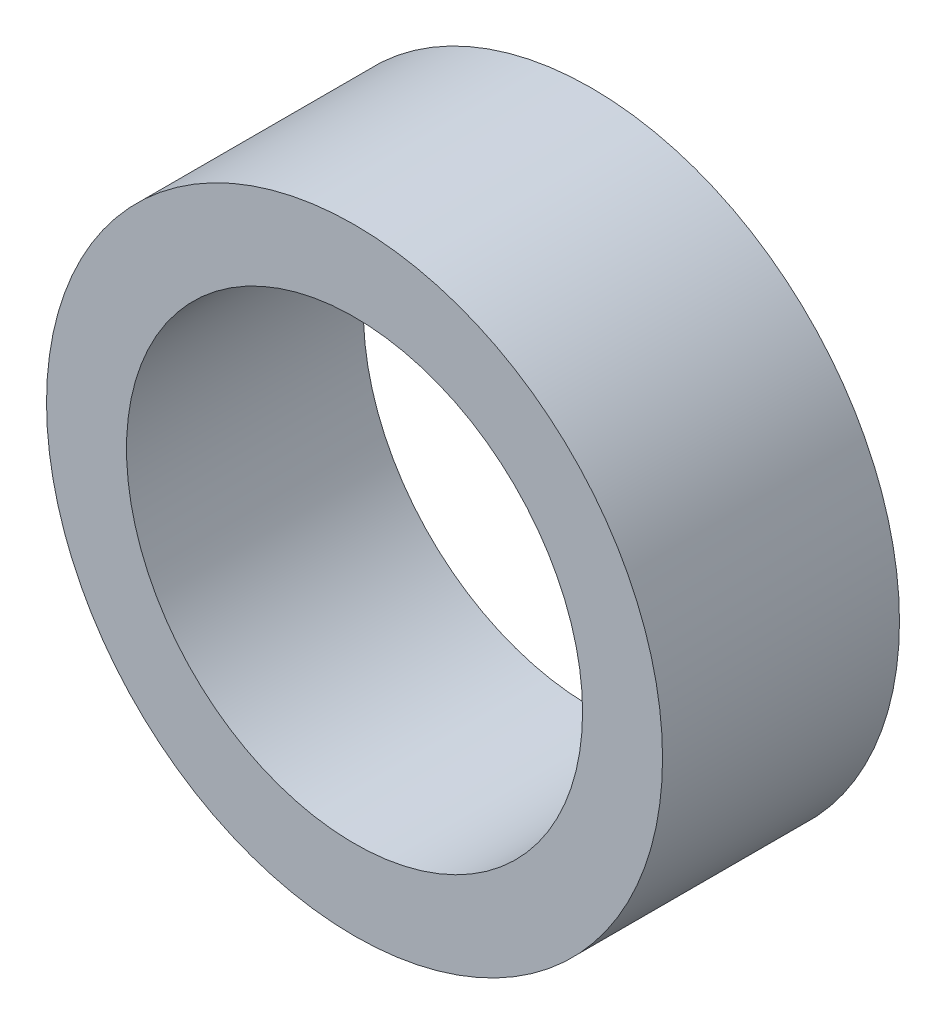
SolidWorks part; units mm, degrees
ref_plane "Piano frontale" through (0, 0, 0) normal (0, 0, 1) x (1, 0, 0)
ref_plane "Piano superiore" through (0, 0, 0) normal (0, 1, 0) x (1, 0, 0)
ref_plane "Piano destro" through (0, 0, 0) normal (1, 0, 0) x (0, 0, -1)
sketch "Sketch1" plane through (0, 0, 0) normal (0, 0, 1) x (1, 0, 0)
  circle A0 centre (0, 0) radius 6.5
  dimension "D1" = 13
extrude "Boss-Extrude1" add sketch "Sketch1" along normal blind 5
sketch "Sketch2" plane through (0, 0, 5) normal (0, 0, 1) x (1, 0, 0)
  circle A0 centre (0, 0) radius 4.8125
  dimension "D1" = 9.625
extrude "Cut-Extrude1" cut sketch "Sketch2" against normal blind 5
